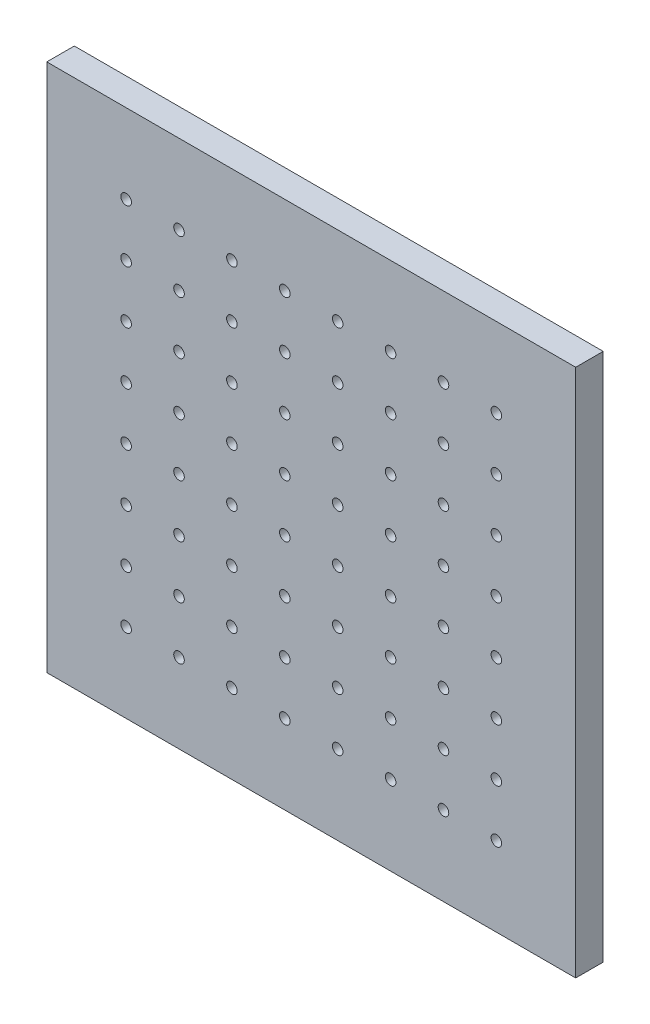
SolidWorks part; units mm, degrees
ref_plane "前视基准面" through (0, 0, 0) normal (0, 0, 1) x (1, 0, 0)
ref_plane "上视基准面" through (0, 0, 0) normal (0, 1, 0) x (1, 0, 0)
ref_plane "右视基准面" through (0, 0, 0) normal (1, 0, 0) x (0, 0, -1)
sketch "草图1" plane through (0, 0, 0) normal (0, 0, 1) x (1, 0, 0)
  line L1 (-125, 125) -> (125, 125)
  line L2 (-125, 125) -> (-125, -125)
  line L3 (-125, -125) -> (125, -125)
  line L4 (125, 125) -> (125, -125)
  line L5 (-125, 125) -> (125, -125) construction
  line L6 (-125, -125) -> (125, 125) construction
  point P0 (0, 0)
  dimension "D1" = 250
  dimension "D2" = 250
extrude "凸台-拉伸1" add sketch "草图1" along normal blind 13
sketch "草图2" plane through (0, 0, 13) normal (0, 0, 1) x (1, 0, 0)
  line L0 (125, 125) -> (-125, 125) construction
  line L1 (-87.5, 87.5) -> (87.5, 87.5) construction
  line L2 (-87.5, 87.5) -> (-87.5, -87.5) construction
  line L3 (-87.5, -87.5) -> (87.5, -87.5) construction
  line L4 (87.5, 87.5) -> (87.5, -87.5) construction
  line L5 (-87.5, 87.5) -> (87.5, -87.5) construction
  line L6 (-87.5, -87.5) -> (87.5, 87.5) construction
  line L7 (125, -125) -> (125, 125) construction
  point P0 (0, 0)
  dimension "D1" = 37.5
  dimension "D2" = 37.5
hole_wizard "M6 螺纹孔的螺纹孔钻头1" positions "草图3" profile "草图4" hole size "M6" standard "DIN" end condition through all
sketch "草图3" plane through (0, 0, 13) normal (0, 0, 1) x (1, 0, 0)
  point P0 (-87.5, -87.5)
sketch "草图4" plane through (-87.5, -87.5, 13) normal (1, 0, 0) x (0, -1, 0)
  line L0 (0, 0) -> (0, 13)
  line L1 (0, 13) -> (2.5, 13)
  line L2 (2.5, 13) -> (2.5, 0)
  line L5 (2.5, 0) -> (0, 0)
  line L11 (0, -6.35) -> (0, 107.95) construction
  dimension "通孔孔直径" = 5
  dimension "通孔孔深度" = 13
pattern_linear "阵列(线性)1" count 8 spacing 25 along (0, 1, 0) count 8 spacing 25 along (1, 0, 0) of "M6 螺纹孔的螺纹孔钻头1"
